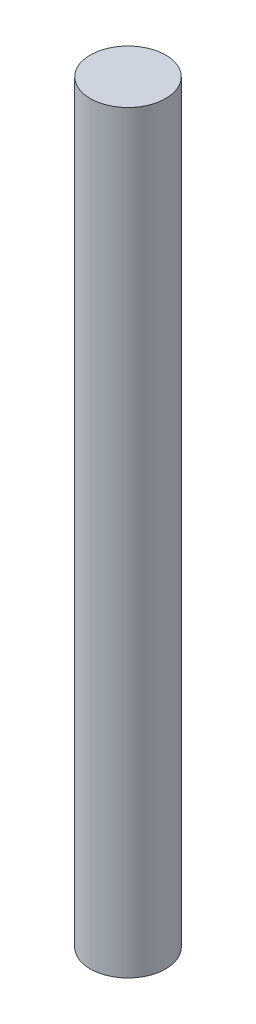
SolidWorks part; units mm, degrees
ref_plane "Front Plane" through (0, 0, 0) normal (0, 0, 1) x (1, 0, 0)
ref_plane "Top Plane" through (0, 0, 0) normal (0, 1, 0) x (1, 0, 0)
ref_plane "Right Plane" through (0, 0, 0) normal (1, 0, 0) x (0, 0, -1)
sketch "Sketch1" plane through (0, 0, 0) normal (0, 1, 0) x (1, 0, 0)
  circle A0 centre (0, 0) radius 0.75
  dimension "D1" = 1.5
extrude "Boss-Extrude1" add sketch "Sketch1" along normal blind 15
